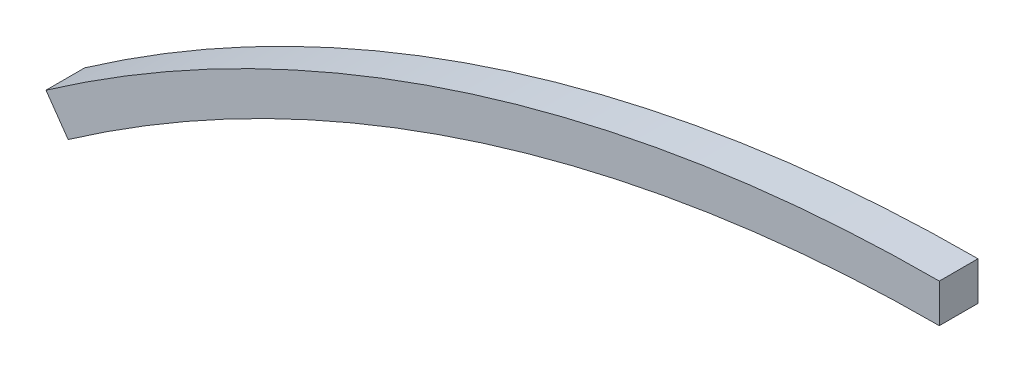
SolidWorks part; units mm, degrees
ref_plane "Plan de face" through (0, 0, 0) normal (0, 0, 1) x (1, 0, 0)
ref_plane "Plan de dessus" through (0, 0, 0) normal (0, 1, 0) x (1, 0, 0)
ref_plane "Plan de droite" through (0, 0, 0) normal (1, 0, 0) x (0, 0, -1)
sketch "Esquisse1" plane through (0, 0, 0) normal (0, 0, 1) x (1, 0, 0)
  line L0 (-46.2076, 66.0834) -> (-45.0615, 64.4444)
  line L1 (0, 78.636) -> (0, 80.636)
  arc A0 (0, 78.636) -> (-45.0615, 64.4444) centre (0, 0) ccw
  arc A1 (0, 80.636) -> (-46.2076, 66.0834) centre (0, 0) ccw
  dimension "D1" = 2
extrude "Boss.-Extru.1" add sketch "Esquisse1" along normal blind 2
